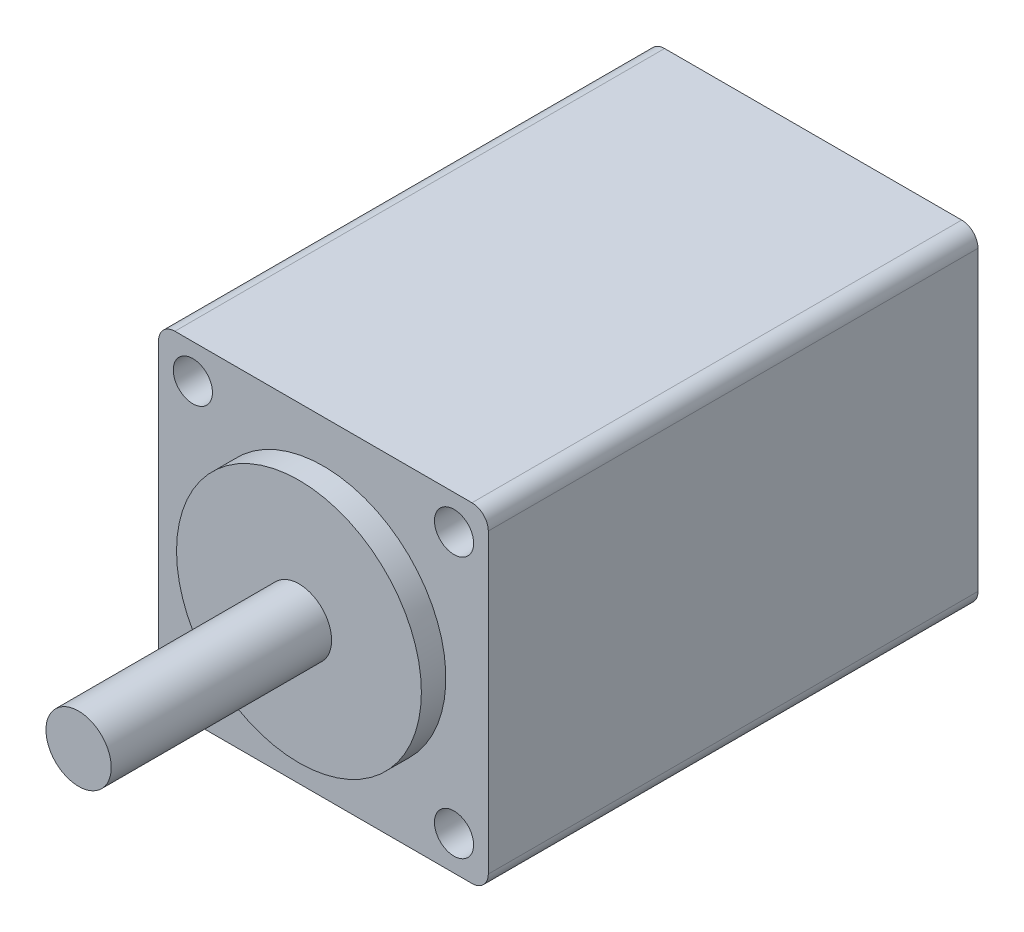
SolidWorks part; units mm, degrees
ref_plane "Plan de face" through (0, 0, 0) normal (0, 0, 1) x (1, 0, 0)
ref_plane "Plan de dessus" through (0, 0, 0) normal (0, 1, 0) x (1, 0, 0)
ref_plane "Plan de droite" through (0, 0, 0) normal (1, 0, 0) x (0, 0, -1)
sketch "Esquisse1" plane through (0, 0, 0) normal (0, 0, 1) x (1, 0, 0)
  line L0 (-10.1, 10.1) -> (10.1, -10.1) construction
  line L1 (-10.1, -10.1) -> (10.1, -10.1)
  line L2 (-10.1, -10.1) -> (-10.1, 10.1)
  line L3 (-10.1, 10.1) -> (10.1, 10.1)
  line L4 (10.1, -10.1) -> (10.1, 10.1)
  dimension "D1" = 20.2
extrude "Boss.-Extru.1" add sketch "Esquisse1" against normal blind 30
sketch "Esquisse2" plane through (0, 0, 0) normal (0, 0, 1) x (1, 0, 0)
  circle A0 centre (0, 0) radius 7.5
  dimension "D1" = 15
extrude "Boss.-Extru.2" add sketch "Esquisse2" along normal blind 1.5
sketch "Esquisse3" plane through (0, 0, 1.5) normal (0, 0, 1) x (1, 0, 0)
  circle A0 centre (0, 0) radius 2
  dimension "D1" = 4
extrude "Boss.-Extru.4" add sketch "Esquisse3" along normal blind 13.5
sketch "Esquisse4" plane through (0, 0, 0) normal (0, 0, 1) x (1, 0, 0)
  line L0 (0, 10.1) -> (0, -10.1) construction
  line L1 (10.1, 10.1) -> (-10.1, 10.1) construction
  line L2 (-10.1, -10.1) -> (10.1, -10.1) construction
  line L3 (-10.1, 0) -> (10.1, 0) construction
  line L4 (-10.1, 10.1) -> (-10.1, -10.1) construction
  line L5 (10.1, -10.1) -> (10.1, 10.1) construction
  circle A0 centre (-8, 8) radius 1.2
  circle A1 centre (8, 8) radius 1.2
  circle A2 centre (8, -8) radius 1.2
  circle A3 centre (-8, -8) radius 1.2
  dimension "D3" = 2.4
  dimension "D1" = 16
  dimension "D2" = 16
extrude "Enlèv. mat.-Extru.1" cut sketch "Esquisse4" against normal blind 3.5
fillet "Congé1" radius 1 4 edges at (-10.1, 10.1, -15) (-10.1, -10.1, -15) (10.1, -10.1, -15) (10.1, 10.1, -15)
